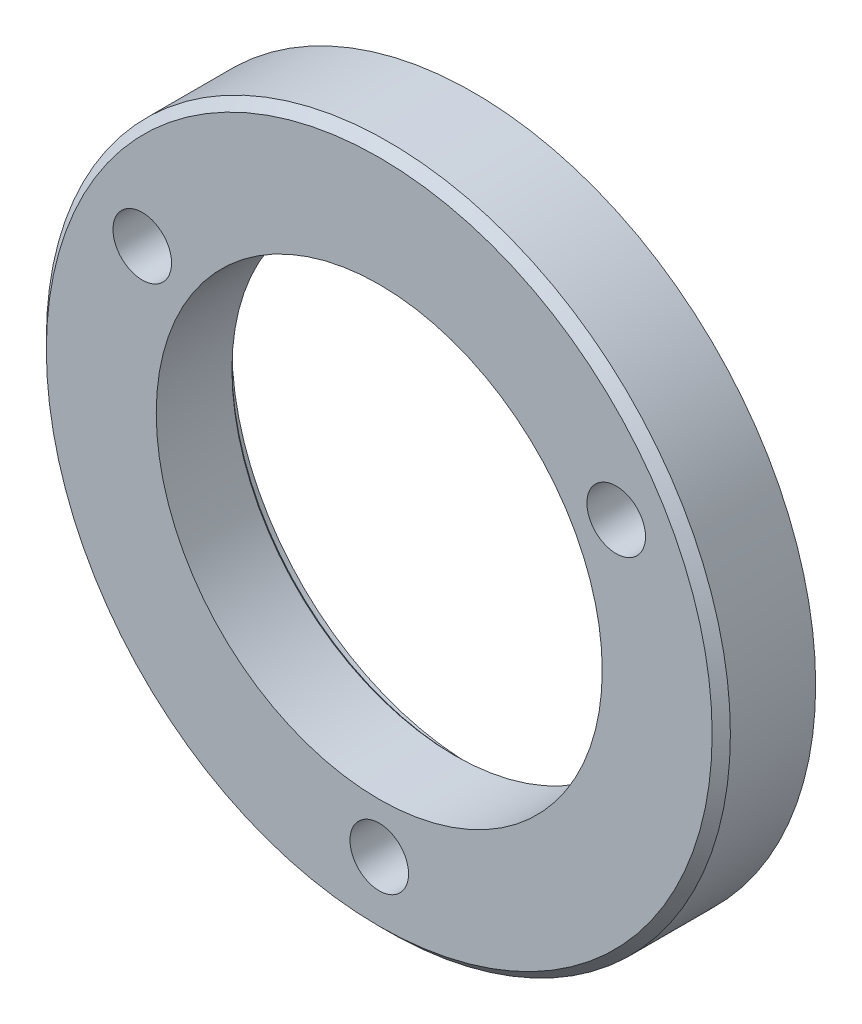
SolidWorks part; units mm, degrees
material "PEEK"
ref_plane "Front" through (0, 0, 0) normal (0, 0, 1) x (1, 0, 0)
ref_plane "Top" through (0, 0, 0) normal (0, 1, 0) x (1, 0, 0)
ref_plane "Right" through (0, 0, 0) normal (1, 0, 0) x (0, 0, -1)
sketch "Sketch1" plane through (0, 0, 0) normal (0, 0, 1) x (1, 0, 0)
  circle A0 centre (-8.5145, 61.389) radius 12.4206
  circle A1 centre (-8.5145, 61.389) radius 19.05
  point P0 (0, 0)
  dimension "D3" = 24.8412
  dimension "D4" = 38.1
extrude "Boss-Extrude1" add sketch "Sketch1" along normal blind 4.3688
sketch "Sketch4" plane through (0, 0, 0) normal (0, 0, -1) x (-1, 0, 0)
  circle A0 centre (8.5145, 61.389) radius 13.462
  circle A1 centre (8.5145, 61.389) radius 19.05
  dimension "D1" = 38.1
  dimension "D2" = 26.924
extrude "Boss-Extrude2" add sketch "Sketch4" along normal blind 0.889
hole_wizard "#4 Clearance Hole1" positions "Sketch3" profile "Sketch2" hole size "#4" standard "Ansi Inch" end condition through all
sketch "Sketch3" plane through (-12.9132, 9.2478, 4.3688) normal (0, 0, 1) x (1, 0, 0)
  line L0 (4.3987, 52.1826) -> (17.5969, 59.8026) construction
  line L2 (4.3987, 52.1826) -> (4.3987, 36.9426) construction
  circle A0 centre (4.3987, 52.1826) radius 15.24 construction
  point P0 (17.5969, 59.8026)
  point P1 (-8.7996, 59.8026)
  point P3 (4.3987, 36.9426)
  dimension "D1" = 30.48
  dimension "D2" = 120
sketch "Sketch2" plane through (4.6837, 69.0504, 4.3688) normal (1, 0, 0) x (0, -1, 0)
  line L0 (0, 0) -> (0, 5.2578)
  line L1 (0, 5.2578) -> (1.6319, 5.2578)
  line L2 (1.6319, 5.2578) -> (1.6319, 0)
  line L5 (1.6319, 0) -> (0, 0)
  line L11 (0, -6.35) -> (0, 107.95) construction
  dimension "Thru Hole Dia." = 3.2639
  dimension "Thru Hole Depth" = 5.2578
chamfer "Chamfer1" distance 0.1524 angle 45 1 edges at (3.9061, 61.389, 0)
chamfer "Chamfer2" distance 0.508 angle 45 1 edges at (10.5355, 61.389, 4.3688)
